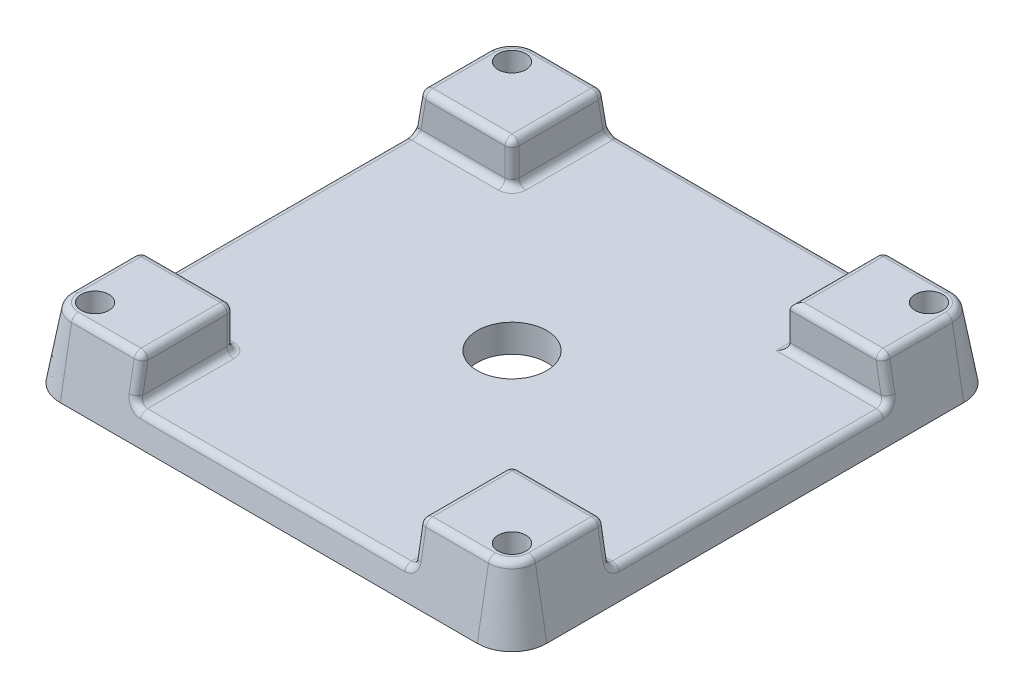
SolidWorks part; units mm, degrees
ref_plane "前视" through (0, 0, 0) normal (0, 0, 1) x (1, 0, 0)
ref_plane "上视" through (0, 0, 0) normal (0, 1, 0) x (1, 0, 0)
ref_plane "右视" through (0, 0, 0) normal (1, 0, 0) x (0, 0, -1)
sketch "草图1" plane through (0, 0, 0) normal (0, 1, 0) x (1, 0, 0)
  line L1 (-30, 35) -> (30, 35)
  line L2 (-35, 30) -> (-35, -30)
  line L3 (-30, -35) -> (30, -35)
  line L4 (35, 30) -> (35, -30)
  line L5 (-35, 35) -> (35, -35) construction
  line L6 (-35, -35) -> (35, 35) construction
  arc A0 (-35, -30) -> (-30, -35) centre (-30, -30) ccw
  arc A1 (30, -35) -> (35, -30) centre (30, -30) ccw
  arc A2 (-30, 35) -> (-35, 30) centre (-30, 30) ccw
  arc A3 (30, 35) -> (35, 30) centre (30, 30) cw
  point P0 (0, 0)
  dimension "D3" = 5
  dimension "D1" = 70
  dimension "D2" = 70
extrude "凸台-拉伸1" add sketch "草图1" along normal blind 10 draft 10
sketch "草图2" plane through (0, 0, 0) normal (0, -1, 0) x (1, 0, 0)
  line L1 (-30, 30) -> (30, 30) construction
  line L2 (-30, 30) -> (-30, -30) construction
  line L3 (-30, -30) -> (30, -30) construction
  line L4 (30, 30) -> (30, -30) construction
  line L5 (-30, 30) -> (30, -30) construction
  line L6 (-30, -30) -> (30, 30) construction
  circle A0 centre (30, 30) radius 2
  circle A1 centre (-30, 30) radius 2
  circle A2 centre (-30, -30) radius 2
  circle A3 centre (30, -30) radius 2
  point P0 (0, 0)
  dimension "D3" = 4
  dimension "D1" = 60
  dimension "D2" = 60
extrude "切除-拉伸1" cut sketch "草图2" against normal blind 26
sketch "草图3" plane through (0, 0, 0) normal (0, -1, 0) x (1, 0, 0)
  circle A0 centre (0, 0) radius 5
  dimension "D1" = 10
extrude "切除-拉伸2" cut sketch "草图3" against normal blind 26
sketch "草图4" plane through (0, 0, 0) normal (0, 0, 1) x (1, 0, 0)
  line L0 (-30, 0) -> (30, 0) construction
  line L1 (-20, 30.0338) -> (20, 30.0338)
  line L2 (-20, 30.0338) -> (-20, 4)
  line L3 (-20, 4) -> (20, 4)
  line L4 (20, 30.0338) -> (20, 4)
  line L5 (-20, 30.0338) -> (20, 4) construction
  line L6 (-20, 4) -> (20, 30.0338) construction
  point P0 (0, 17.0169)
  dimension "D1" = 40
  dimension "D2" = 4
extrude "切除-拉伸3" cut sketch "草图4" against normal mid plane 100
sketch "草图6" plane through (0, 0, 0) normal (1, 0, 0) x (0, 0, -1)
  line L0 (-30, 0) -> (30, 0) construction
  line L1 (-20, 37.3767) -> (20, 37.3767)
  line L2 (-20, 37.3767) -> (-20, 4)
  line L3 (-20, 4) -> (20, 4)
  line L4 (20, 37.3767) -> (20, 4)
  line L5 (-20, 37.3767) -> (20, 4) construction
  line L6 (-20, 4) -> (20, 37.3767) construction
  point P0 (0, 20.6883)
  dimension "D1" = 4
  dimension "D2" = 40
extrude "切除-拉伸4" cut sketch "草图6" against normal mid plane 100
fillet "圆角1" radius 1 43 edges at (-20, 7, 33.7657) (-33.7657, 7, -20) (0, 4, 34.2947) (-20, 4, 27.1473) (-34.2947, 4, 0) (20, 4, 27.1473) (-27.1473, 4, -20) (20, 7, -33.7657) (-25, 10, 33.2367) (-32.2887, 10, 32.2887) (25, 10, 33.2367) (32.2887, 10, 32.2887) (33.2367, 10, -25) (32.2887, 10, -32.2887) (-33.2367, 10, -25) (-32.2887, 10, -32.2887) (-20, 7, 20) (-33.7657, 7, 20) (-33.2367, 10, 25) (-20, 10, 26.6184) (-27.1473, 4, 20) (-26.6184, 10, 20) (20, 7, 33.7657) (27.1473, 4, 20) (20, 7, 20) (20, 10, 26.6184) (26.6184, 10, 20) (33.2367, 10, 25) (33.7657, 7, 20) (27.1473, 4, -20) (34.2947, 4, 0) (33.7657, 7, -20) (26.6184, 10, -20) (25, 10, -33.2367) (-25, 10, -33.2367) (-26.6184, 10, -20) (-20, 7, -20) (-20, 10, -26.6184) (20, 10, -26.6184) (20, 4, -27.1473) (-20, 4, -27.1473) (0, 4, -34.2947) (-20, 7, -33.7657)
